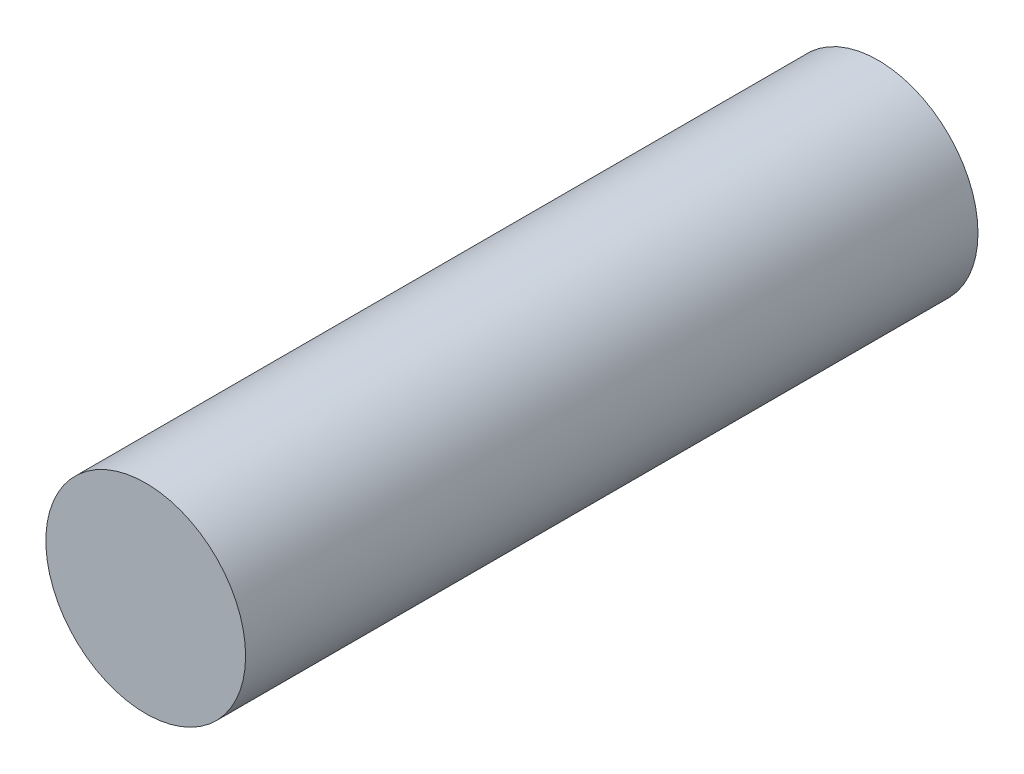
SolidWorks part; units mm, degrees
ref_plane "Front Plane" through (0, 0, 0) normal (0, 0, 1) x (1, 0, 0)
ref_plane "Top Plane" through (0, 0, 0) normal (0, 1, 0) x (1, 0, 0)
ref_plane "Right Plane" through (0, 0, 0) normal (1, 0, 0) x (0, 0, -1)
sketch "Sketch1" plane through (0, 0, 0) normal (0, 0, 1) x (1, 0, 0)
  circle A0 centre (0, 0) radius 6
  dimension "D1" = 12
extrude "Boss-Extrude1" add sketch "Sketch1" along normal blind 44
